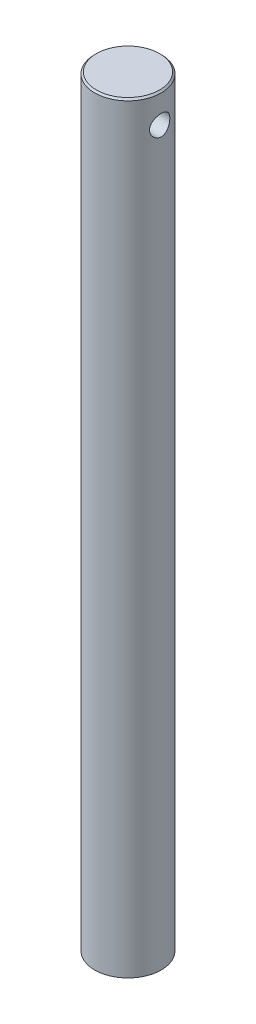
SolidWorks part; units mm, degrees
ref_plane "Front Plane" through (0, 0, 0) normal (0, 0, 1) x (1, 0, 0)
ref_plane "Top Plane" through (0, 0, 0) normal (0, 1, 0) x (1, 0, 0)
ref_plane "Right Plane" through (0, 0, 0) normal (1, 0, 0) x (0, 0, -1)
sketch "Sketch1" plane through (0, 0, 0) normal (0, 1, 0) x (1, 0, 0)
  circle A0 centre (0, 0) radius 10.0013
  dimension "D1" = 20.0025
extrude "Boss-Extrude1" add sketch "Sketch1" along normal blind 203.2
sketch "Sketch2" plane through (0, 203.2, 0) normal (0, 1, 0) x (1, 0, 0)
  circle A0 centre (0, 0) radius 10.0013
extrude "Boss-Extrude2" add sketch "Sketch2" along normal blind 25.7175
sketch "Sketch3" plane through (0, 228.9175, 0) normal (0, 1, 0) x (1, 0, 0)
  line L0 (10.0013, -10.0013) -> (-10.0013, -10.0013)
  line L1 (10.0013, -10.0013) -> (10.0012, 10.0012)
  line L2 (-10.0013, -10.0013) -> (-10.0013, 10.0012)
  line L3 (10.0012, 10.0012) -> (-10.0013, 10.0012)
  line L4 (10.0013, -10.0013) -> (-10.0013, 10.0012) construction
  line L5 (-10.0013, -10.0013) -> (10.0012, 10.0012) construction
  point P1 (0, 0)
ref_plane "Plane1" through (10.0013, 0, 0) normal (1, 0, 0) x (0, 0, -1)
sketch "Sketch4" plane through (10.0013, 0, 0) normal (1, 0, 0) x (0, 0, -1)
  line L0 (0, 228.9175) -> (0, 223.0755)
  line L1 (0, 223.0755) -> (0, 220.0275)
  circle A0 centre (0, 220.0275) radius 3.048
  dimension "D1" = 5.842
  dimension "D2" = 3.048
extrude "Cut-Extrude1" cut sketch "Sketch4" against normal blind 25.4
chamfer "Chamfer1" distance 0.508 1 edges at (0, 228.9175, 10.0013)
